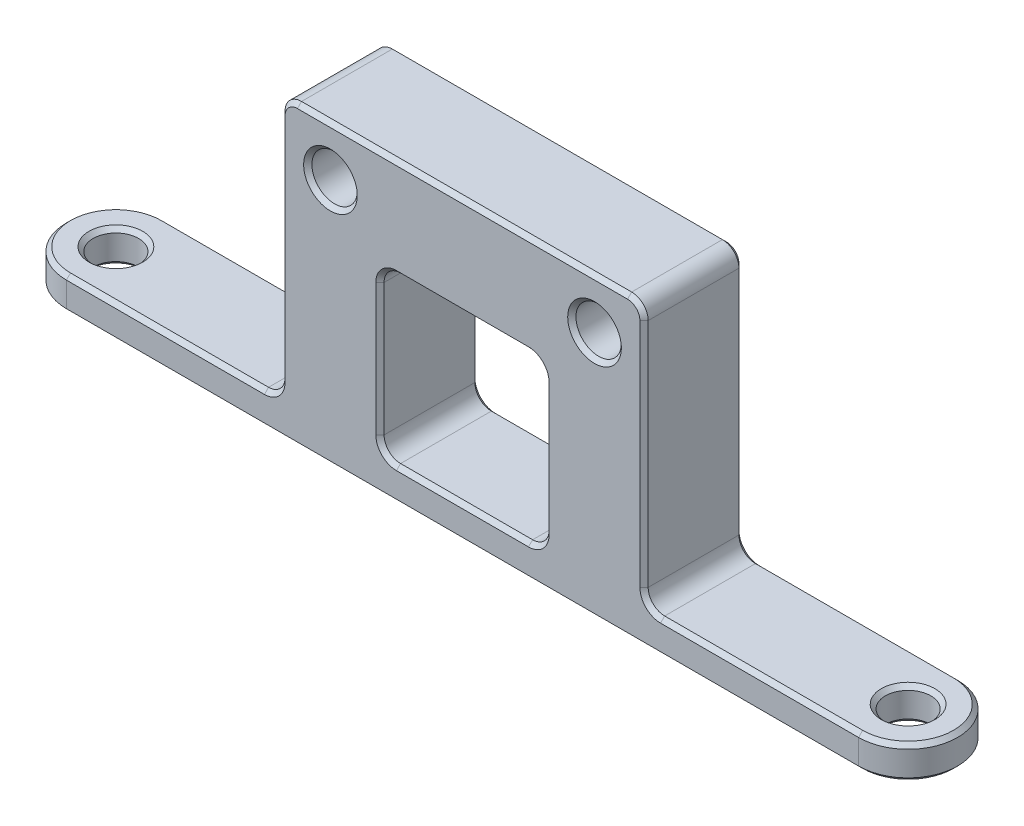
SolidWorks part; units mm, degrees
ref_plane "Front Plane" through (0, 0, 0) normal (0, 0, 1) x (1, 0, 0)
ref_plane "Top Plane" through (0, 0, 0) normal (0, 1, 0) x (1, 0, 0)
ref_plane "Right Plane" through (0, 0, 0) normal (1, 0, 0) x (0, 0, -1)
sketch "Sketch2" plane through (0, 0, 0) normal (0, 1, 0) x (1, 0, 0)
  line L0 (-38.1, 0) -> (38.1, 0) construction
  line L5 (-38.1, 4.7625) -> (38.1, 4.7625)
  line L6 (-38.1, -4.7625) -> (38.1, -4.7625)
  circle A0 centre (-38.1, 0) radius 2.1828
  circle A1 centre (38.1, 0) radius 2.1828
  arc A2 (-38.1, 4.7625) -> (-38.1, -4.7625) centre (-38.1, 0) ccw
  arc A3 (38.1, -4.7625) -> (38.1, 4.7625) centre (38.1, 0) ccw
  point P0 (0, 0)
  point P1 (0, 0)
  dimension "D3" = 4.3656
  dimension "D4" = 4.3656
  dimension "D5" = 4.7625
  dimension "D1" = 38.1
  dimension "D2" = 38.1
extrude "Boss-Extrude1" add sketch "Sketch2" along normal blind 3.175
sketch "Sketch3" plane through (0, 3.175, 0) normal (0, 1, 0) x (1, 0, 0)
  line L0 (38.1, 4.7625) -> (-38.1, 4.7625) construction
  line L1 (-18.4216, -4.7625) -> (18.4216, -4.7625)
  line L2 (-18.4216, -4.7625) -> (-18.4216, 4.7625)
  line L3 (-18.4216, 4.7625) -> (18.4216, 4.7625)
  line L4 (18.4216, -4.7625) -> (18.4216, 4.7625)
  line L5 (-18.4216, -4.7625) -> (18.4216, 4.7625) construction
  line L6 (-18.4216, 4.7625) -> (18.4216, -4.7625) construction
  point P0 (0, 0)
  dimension "D1" = 36.8432
extrude "Boss-Extrude2" add sketch "Sketch3" along normal blind 25.4
sketch "Sketch4" plane through (0, 0, 4.7625) normal (0, 0, 1) x (1, 0, 0)
  line L0 (-18.4216, 28.575) -> (18.4216, 28.575) construction
  line L1 (-38.1, 3.175) -> (-18.4216, 3.175) construction
  line L2 (-18.4216, 28.575) -> (-17.4625, 28.575)
  line L3 (-18.4216, 28.575) -> (-18.4216, 3.175)
  line L4 (-18.4216, 3.175) -> (-17.4625, 3.175)
  line L5 (-17.4625, 28.575) -> (-17.4625, 3.175)
  line L6 (18.4216, 3.175) -> (38.1, 3.175) construction
  line L7 (18.4216, 28.575) -> (17.4625, 28.575)
  line L8 (18.4216, 28.575) -> (18.4216, 3.175)
  line L9 (18.4216, 3.175) -> (17.4625, 3.175)
  line L10 (17.4625, 28.575) -> (17.4625, 3.175)
  line L12 (-7.9375, 3.175) -> (7.9375, 3.175)
  line L13 (-7.9375, 3.175) -> (-7.9375, 19.05)
  line L14 (-7.9375, 19.05) -> (7.9375, 19.05)
  line L15 (7.9375, 3.175) -> (7.9375, 19.05)
  circle A0 centre (-12.7, 23.8125) radius 2.1828
  circle A1 centre (12.7, 23.8125) radius 2.1828
  dimension "D6" = 4.3656
  dimension "D7" = 4.3656
  dimension "D1" = 12.7
  dimension "D2" = 12.7
  dimension "D3" = 4.7625
  dimension "D4" = 4.7625
  dimension "D5" = 4.7625
  dimension "D8" = 4.7625
  dimension "D9" = 4.7625
  dimension "D10" = 4.7625
  dimension "D11" = 4.7625
extrude "Cut-Extrude1" cut sketch "Sketch4" against normal through all both and the other way through all
fillet "Fillet1" radius 1.5875 8 edges at (-17.4625, 28.575, 0) (-17.4625, 3.175, 0) (17.4625, 28.575, 0) (17.4625, 3.175, 0) (-7.9375, 19.05, 0) (7.9375, 19.05, 0) (7.9375, 3.175, 0) (-7.9375, 3.175, 0)
chamfer "Chamfer1" distance 0.3969 angle 45 48 edges at (-14.8828, 23.8125, 4.7625) (-10.5172, 23.8125, -4.7625) (10.5172, 23.8125, 4.7625) (14.8828, 23.8125, -4.7625) (38.1, 3.175, 2.1828) (-38.1, 3.175, 2.1828) (0, 19.05, -4.7625) (-7.4725, 18.585, -4.7625) (7.4725, 18.585, -4.7625) (-7.9375, 11.1125, -4.7625) (7.9375, 11.1125, -4.7625) (-7.4725, 3.64, -4.7625) (7.4725, 3.64, -4.7625) (0, 3.175, -4.7625) (0, 19.05, 4.7625) (7.4725, 18.585, 4.7625) (-7.4725, 18.585, 4.7625) (7.9375, 11.1125, 4.7625) (-7.9375, 11.1125, 4.7625) (7.4725, 3.64, 4.7625) (-7.4725, 3.64, 4.7625) (0, 3.175, 4.7625) (38.1, 0, 2.1828) (-38.1, 0, 2.1828) (0, 0, 4.7625) (42.8625, 0, 0) (0, 0, -4.7625) (-42.8625, 0, 0) (0, 28.575, 4.7625) (16.9975, 28.11, 4.7625) (-16.9975, 28.11, 4.7625) (17.4625, 15.875, 4.7625) (-17.4625, 15.875, 4.7625) (17.9275, 3.64, 4.7625) (-17.9275, 3.64, 4.7625) (28.575, 3.175, 4.7625) (-28.575, 3.175, 4.7625) (42.8625, 3.175, 0) (-42.8625, 3.175, 0) (28.575, 3.175, -4.7625) (-28.575, 3.175, -4.7625) (17.9275, 3.64, -4.7625) (-17.9275, 3.64, -4.7625) (17.4625, 15.875, -4.7625) (-17.4625, 15.875, -4.7625) (16.9975, 28.11, -4.7625) (-16.9975, 28.11, -4.7625) (0, 28.575, -4.7625)
